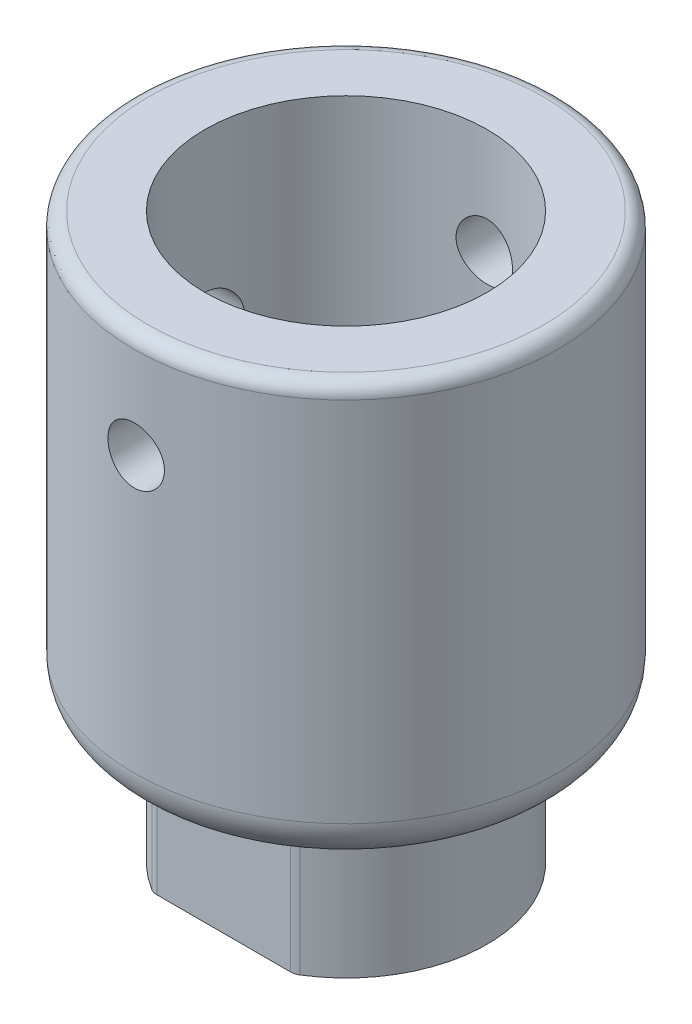
SolidWorks part; units mm, degrees
material "ABS"
ref_plane "Plano frontal" through (0, 0, 0) normal (0, 0, 1) x (1, 0, 0)
ref_plane "Plano superior" through (0, 0, 0) normal (0, 1, 0) x (1, 0, 0)
ref_plane "Plano direito" through (0, 0, 0) normal (1, 0, 0) x (0, 0, -1)
other "Centro da massa"
sketch "Esboço1" plane through (0, 0, 0) normal (0, 1, 0) x (1, 0, 0)
  circle A1 centre (0, 0) radius 15
  dimension "D2" = 30
extrude "Ressalto-extrusão1" add sketch "Esboço1" along normal blind 30
sketch "Esboço2" plane through (0, 30, 0) normal (0, 1, 0) x (1, 0, 0)
  circle A0 centre (0, 0) radius 10
  dimension "D1" = 20
extrude "Corte-extrusão1" cut sketch "Esboço2" against normal blind 15
sketch "Esboço3" plane through (0, 0, 0) normal (0, -1, 0) x (1, 0, 0)
  line L0 (0, 10) -> (0, -10) construction
  line L1 (-5, -8.6603) -> (5, -8.6603)
  line L2 (-5, 8.6603) -> (5, 8.6603)
  arc A0 (-5, 8.6603) -> (-5, -8.6603) centre (0, 0) ccw
  arc A1 (5, -8.6603) -> (5, 8.6603) centre (0, 0) ccw
  dimension "D1" = 20
  dimension "D2" = 10
extrude "Ressalto-extrusão2" add sketch "Esboço3" along normal blind 10
sketch "Esboço4" plane through (0, -10, 0) normal (0, -1, 0) x (1, 0, 0)
  circle A0 centre (0, 0) radius 1
  dimension "D1" = 2
extrude "Corte-extrusão2" cut sketch "Esboço4" against normal blind 5
sketch "Esboço5" plane through (0, 15, 0) normal (0, 1, 0) x (1, 0, 0)
  circle A0 centre (0, 0) radius 3.5
  dimension "D1" = 7
extrude "Corte-extrusão3" cut sketch "Esboço5" against normal blind 20
sketch "Esboço6" plane through (0, 0, 0) normal (0, 0, 1) x (1, 0, 0)
  line L0 (15, 30) -> (-15, 30) construction
  circle A0 centre (0, 22.5) radius 2
  dimension "D2" = 4
  dimension "D1" = 7.5
extrude "Corte-extrusão4" cut sketch "Esboço6" against normal through all both and the other way through all
sketch "Esboço7" plane through (0, 0, 0) normal (1, 0, 0) x (0, 0, -1)
  line L0 (15, 30) -> (-15, 30) construction
  circle A0 centre (0, 17.5) radius 2.5
  dimension "D1" = 5
  dimension "D2" = 12.5
extrude "Corte-extrusão5" cut sketch "Esboço7" against normal through all
sketch "Esboço9" plane through (0, -10, 0) normal (0, -1, 0) x (1, 0, 0)
  line L0 (2.6458, 3) -> (2.6458, -3)
  arc A0 (2.6458, 3) -> (2.6458, -3) centre (0, 0) ccw
  dimension "D1" = 8
  dimension "D2" = 6
extrude "Corte-extrusão6" cut sketch "Esboço9" against normal blind 4
fillet "Filete1" radius 1 1 edges at (0, 30, 15)
fillet "Filete2" radius 3 1 edges at (0, 0, 15)
fillet "Filete4" radius 1 4 edges at (-5, -5, 8.6603) (5, -5, 8.6603) (5, -5, -8.6603) (-5, -5, -8.6603)
